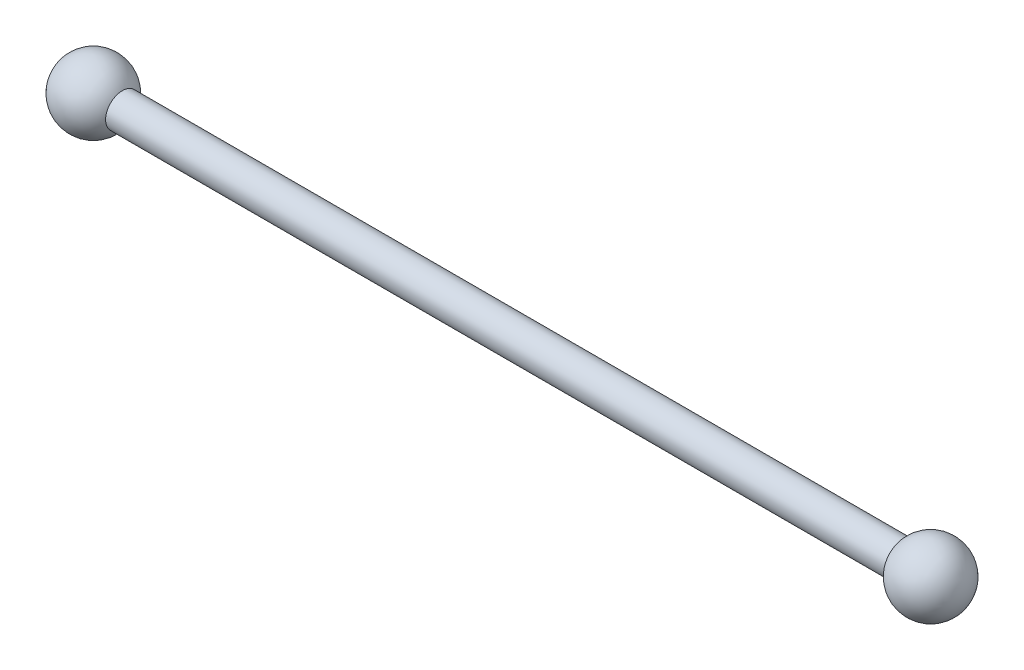
SolidWorks part; units mm, degrees
ref_plane "Front Plane" through (0, 0, 0) normal (0, 0, 1) x (1, 0, 0)
ref_plane "Top Plane" through (0, 0, 0) normal (0, 1, 0) x (1, 0, 0)
ref_plane "Right Plane" through (0, 0, 0) normal (1, 0, 0) x (0, 0, -1)
sketch "Sketch1" plane through (0, 0, 0) normal (1, 0, 0) x (0, 0, -1)
  circle A0 centre (0, 0) radius 5
  dimension "D1" = 10
extrude "Boss-Extrude1" add sketch "Sketch1" along normal mid plane 250
sketch "Sketch2" plane through (125, 0, 0) normal (1, 0, 0) x (0, 0, -1)
  line L0 (0, 10) -> (0, -10)
  arc A0 (0, -10) -> (0, 10) centre (0, 0) ccw
  dimension "D1" = 10
revolve "Revolve1" add sketch "Sketch2" angle 360 about L0
mirror "Mirror1" about plane through (0, 0, 0) normal (1, 0, 0) of "Revolve1"
